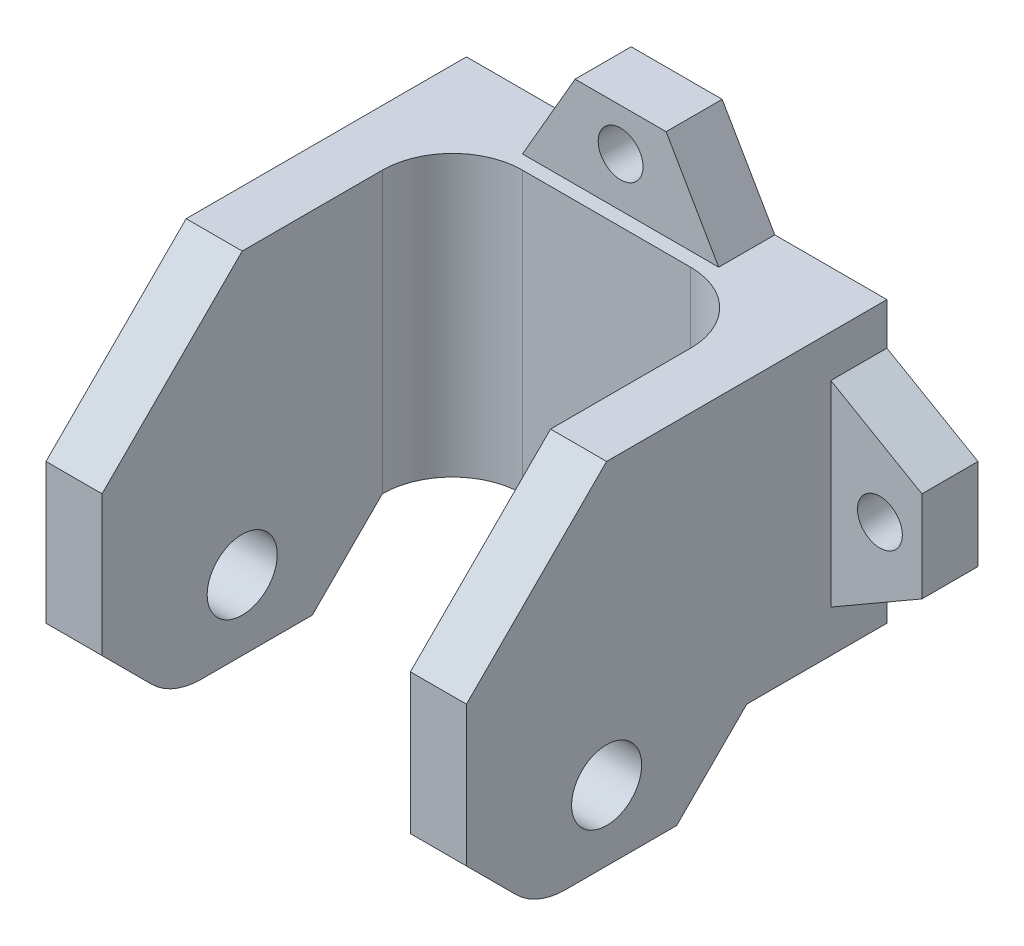
SolidWorks part; units mm, degrees
ref_plane "前视基准面" through (0, 0, 0) normal (0, 0, 1) x (1, 0, 0)
ref_plane "上视基准面" through (0, 0, 0) normal (0, 1, 0) x (1, 0, 0)
ref_plane "右视基准面" through (0, 0, 0) normal (1, 0, 0) x (0, 0, -1)
sketch "Sketch1" plane through (0, 0, 0) normal (0, 0, 1) x (1, 0, 0)
  line L0 (0, 285) -> (0, -299.6017) construction
  line L1 (-15, -45) -> (15, -45)
  line L2 (-15, -45) -> (-15, -85)
  line L3 (-15, -85) -> (15, -85)
  line L4 (15, -45) -> (15, -85)
  line L5 (225, 285) -> (-225, 285) construction
  line L6 (-115, -285) -> (115, -285) construction
  point P9 (0, -45)
  dimension "D1" = 30
  dimension "D2" = 40
  dimension "D3" = 200
extrude "Boss-Extrude1" add sketch "Sketch1" along normal blind 5
sketch "Sketch2" plane through (0, 0, 5) normal (0, 0, 1) x (1, 0, 0)
  line L0 (-15, -85) -> (15, -85) construction
  line L1 (-15, -45) -> (-11, -45)
  line L2 (-15, -45) -> (-15, -85)
  line L3 (-15, -85) -> (-11, -85)
  line L4 (-11, -45) -> (-11, -85)
  line L6 (15, -45) -> (11, -45)
  line L7 (15, -45) -> (15, -85)
  line L8 (15, -85) -> (11, -85)
  line L9 (11, -45) -> (11, -85)
  dimension "D1" = 4
  dimension "D2" = 4
extrude "Boss-Extrude2" add sketch "Sketch2" along normal blind 25
chamfer "Chamfer1" distance 10 angle 45 4 edges at (13, -85, 30) (-13, -85, 30) (13, -45, 30) (-13, -45, 30)
sketch "Sketch3" plane through (-15, 0, 0) normal (-1, 0, 0) x (0, 0, 1)
  line L0 (20, -45) -> (0, -45) construction
  line L1 (30, -55) -> (30, -75) construction
  circle A0 centre (20, -65) radius 2.5
  dimension "D1" = 20
  dimension "D2" = 5
  dimension "D3" = 10
extrude "Cut-Extrude1" cut sketch "Sketch3" against normal blind 76
sketch "Sketch4" plane through (-15, 0, 0) normal (-1, 0, 0) x (0, 0, 1)
  line L0 (30, -70) -> (15, -70)
  line L1 (30, -55) -> (30, -75) construction
  line L2 (15, -70) -> (10, -65)
  line L3 (10, -65) -> (0, -65)
  line L4 (0, -45) -> (0, -85) construction
  line L5 (30, -70) -> (31.2179, -87.2551)
  line L6 (31.2179, -87.2551) -> (-4.9062, -89.8049)
  line L7 (-4.9062, -89.8049) -> (0, -65)
  line L8 (20, -45) -> (5, -45) construction
  dimension "D1" = 25
  dimension "D2" = 5
  dimension "D3" = 45
  dimension "D4" = 10
extrude "Cut-Extrude2" cut sketch "Sketch4" against normal blind 76
chamfer "Chamfer2" distance 5 angle 45 2 edges at (-13, -70, 30) (13, -70, 30)
fillet "Fillet1" radius 5 2 edges at (11, -55, 5) (-11, -55, 5)
fillet "Fillet2" radius 5 2 edges at (13, -70, 25) (-13, -70, 25)
sketch "Sketch5" plane through (0, 0, 0) normal (0, 0, -1) x (-1, 0, 0)
  line L0 (7, -45) -> (3.2472, -38.5)
  line L1 (11, -45) -> (6, -45) construction
  line L2 (3.2472, -38.5) -> (-3.2472, -38.5)
  line L3 (-3.2472, -38.5) -> (-7, -45)
  line L4 (-6, -45) -> (-11, -45) construction
  line L5 (-7, -45) -> (7, -45)
  line L6 (15, -48) -> (21.5, -51.7528)
  line L7 (15, -55) -> (15, -45) construction
  line L8 (21.5, -51.7528) -> (21.5, -58.2472)
  line L9 (21.5, -58.2472) -> (15, -62)
  line L10 (15, -55) -> (15, -65) construction
  line L11 (15, -62) -> (15, -48)
  line L12 (0, -45) -> (0, -65) construction
  line L13 (-6, -65) -> (6, -65) construction
  line L14 (-15, -62) -> (-15, -48)
  line L15 (-21.5, -58.2472) -> (-15, -62)
  line L16 (-21.5, -51.7528) -> (-21.5, -58.2472)
  line L17 (-15, -48) -> (-21.5, -51.7528)
  line L18 (15, -45) -> (11, -45) construction
  circle A0 centre (0, -41.5) radius 1.6
  circle A1 centre (18.5, -55) radius 1.6
  circle A2 centre (-18.5, -55) radius 1.6
  dimension "D6" = 3.2
  dimension "D7" = 3
  dimension "D8" = 3
  dimension "D1" = 60
  dimension "D2" = 6.5
  dimension "D3" = 7
  dimension "D4" = 7
  dimension "D5" = 3
  dimension "D9" = 7
  dimension "D10" = 7
extrude "Boss-Extrude3" add sketch "Sketch5" against normal blind 4 separate body
